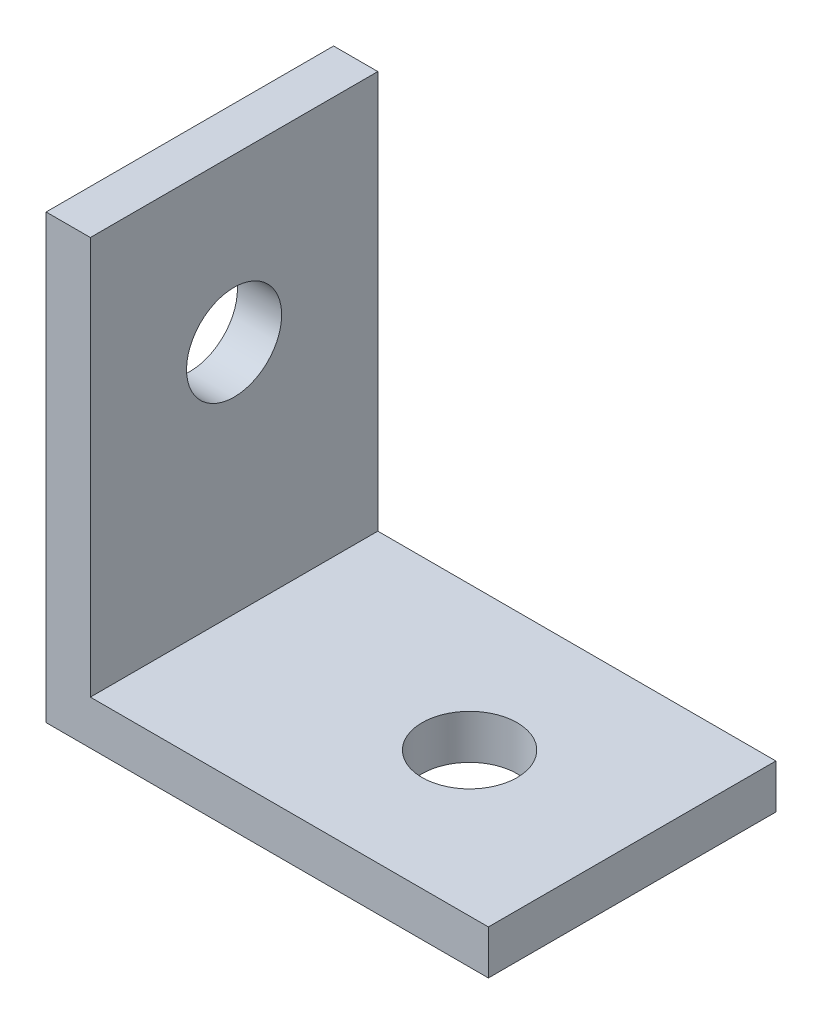
SolidWorks part; units mm, degrees
ref_plane "Front Plane" through (0, 0, 0) normal (0, 0, 1) x (1, 0, 0)
ref_plane "Top Plane" through (0, 0, 0) normal (0, 1, 0) x (1, 0, 0)
ref_plane "Right Plane" through (0, 0, 0) normal (1, 0, 0) x (0, 0, -1)
sketch "Sketch1" plane through (0, 0, 0) normal (0, 0, 1) x (1, 0, 0)
  line L0 (0, 20) -> (0, 0)
  line L1 (0, 0) -> (20, 0)
  line L2 (20, 0) -> (20, 2)
  line L3 (20, 2) -> (2, 2)
  line L4 (2, 2) -> (2, 20)
  line L5 (2, 20) -> (0, 20)
  dimension "D1" = 2
  dimension "D2" = 2
  dimension "D3" = 20
  dimension "D4" = 20
extrude "Boss-Extrude1" add sketch "Sketch1" along normal blind 13
sketch "Sketch2" plane through (0, 0, 0) normal (-1, 0, 0) x (0, 0, 1)
  line L1 (13, 20) -> (0, 20) construction
  circle A0 centre (6.5, 12.65) radius 2.15
  point P4 (6.5, 20)
  point P5 (0, 0)
  dimension "D2" = 4.3
  dimension "D1" = 5.2
extrude "Cut-Extrude1" cut sketch "Sketch2" against normal through all
sketch "Sketch3" plane through (0, 0, 0) normal (0, -1, 0) x (1, 0, 0)
  line L0 (20, 13) -> (20, 0) construction
  circle A0 centre (12.65, 6.5) radius 2.15
  point P4 (20, 6.5)
  point P5 (0, 0)
  dimension "D1" = 4.3
  dimension "D2" = 5.2
extrude "Cut-Extrude2" cut sketch "Sketch3" against normal through all contours A0
equation "\"D2@Sketch1\"=\"D1@Sketch1\""
equation "\"D4@Sketch1\"=\"D3@Sketch1\""
